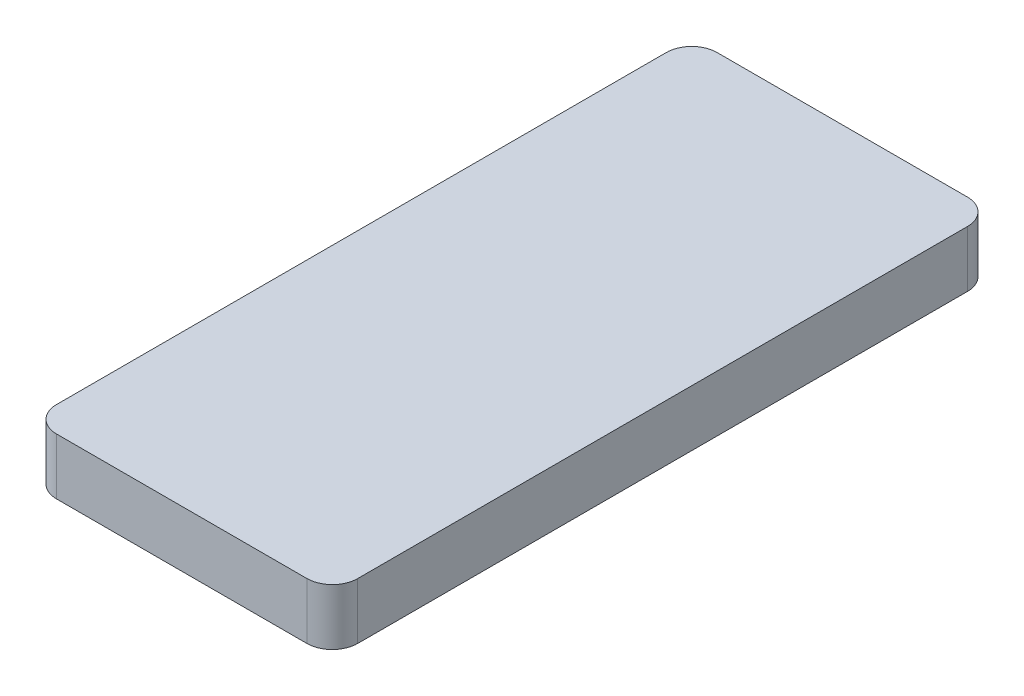
SolidWorks part; units mm, degrees
material "PP Кополимер"
ref_plane "Спереди" through (0, 0, 0) normal (0, 0, 1) x (1, 0, 0)
ref_plane "Сверху" through (0, 0, 0) normal (0, 1, 0) x (1, 0, 0)
ref_plane "Справа" through (0, 0, 0) normal (1, 0, 0) x (0, 0, -1)
sketch "Эскиз2" plane through (0, 0, 0) normal (0, 1, 0) x (1, 0, 0)
  line L1 (-7, 0) -> (-76, 0)
  line L2 (0, 7) -> (0, 175)
  line L3 (-7, 182) -> (-76, 182)
  line L4 (-83, 7) -> (-83, 175)
  arc A0 (-7, 0) -> (0, 7) centre (-7, 7) ccw
  arc A1 (-76, 0) -> (-83, 7) centre (-76, 7) cw
  arc A2 (-76, 182) -> (-83, 175) centre (-76, 175) ccw
  arc A3 (0, 175) -> (-7, 182) centre (-7, 175) ccw
  point P7 (0, 0)
  point P12 (-83, 182)
  point P15 (0, 182)
  dimension "D3" = 7
  dimension "D1" = 182
  dimension "D2" = 83
extrude "Бобышка-Вытянуть1" add sketch "Эскиз2" along normal blind 15.5
shell "Оболочка1" thickness 2
